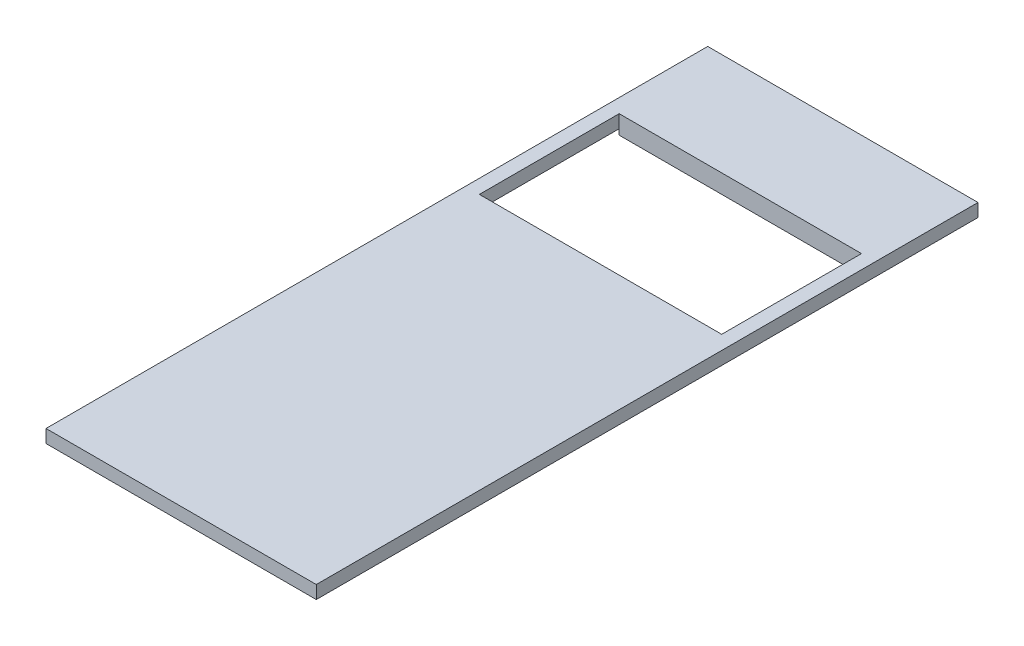
SolidWorks part; units mm, degrees
ref_plane "Front" through (0, 0, 0) normal (0, 0, 1) x (1, 0, 0)
ref_plane "Top" through (0, 0, 0) normal (0, 1, 0) x (1, 0, 0)
ref_plane "Right" through (0, 0, 0) normal (1, 0, 0) x (0, 0, -1)
sketch "Sketch1" plane through (0, 11.5, 0) normal (0, 1, 0) x (1, 0, 0)
  line L1 (1.5, 69.5) -> (27.5, 69.5)
  line L2 (1.5, 69.5) -> (1.5, 1.5)
  line L3 (1.5, 1.5) -> (27.5, 1.5)
  line L4 (27.5, 69.5) -> (27.5, 1.5)
  line L5 (1.5, 69.5) -> (27.5, 1.5) construction
  line L6 (1.5, 1.5) -> (27.5, 69.5) construction
  point P4 (14.5, 35.5)
extrude "Boss-Extrude1" add sketch "Sketch1" against normal blind 0.6
sketch "Sketch2" plane through (0, 11.5, 0) normal (0, 1, 0) x (1, 0, 0)
  line L1 (0, 0) -> (29, 0)
  line L2 (0, 0) -> (0, 71)
  line L3 (0, 71) -> (29, 71)
  line L4 (29, 0) -> (29, 71)
  line L5 (0, 0) -> (29, 71) construction
  line L6 (0, 71) -> (29, 0) construction
  point P4 (14.5, 35.5)
extrude "Boss-Extrude2" add sketch "Sketch2" along normal blind 1.4
sketch "Sketch3" plane through (0, 10.9, 0) normal (0, -1, 0) x (1, 0, 0)
  line L0 (14.5, 0) -> (14.5, -71) construction
  line L1 (0, 0) -> (29, 0) construction
  line L2 (29, -71) -> (0, -71) construction
  line L3 (27.5, -69.5) -> (1.5, -69.5) construction
  line L4 (1.5, -45) -> (27.5, -45)
  line L5 (1.5, -45) -> (1.5, -60)
  line L6 (1.5, -60) -> (27.5, -60)
  line L7 (27.5, -45) -> (27.5, -60)
  line L8 (1.5, -45) -> (27.5, -60) construction
  line L9 (1.5, -60) -> (27.5, -45) construction
  line L10 (27.5, -1.5) -> (27.5, -69.5) construction
  point P6 (14.5, -52.5)
  dimension "D1" = 9.5
  dimension "D2" = 15
extrude "Cut-Extrude1" cut sketch "Sketch3" against normal blind 15.4
